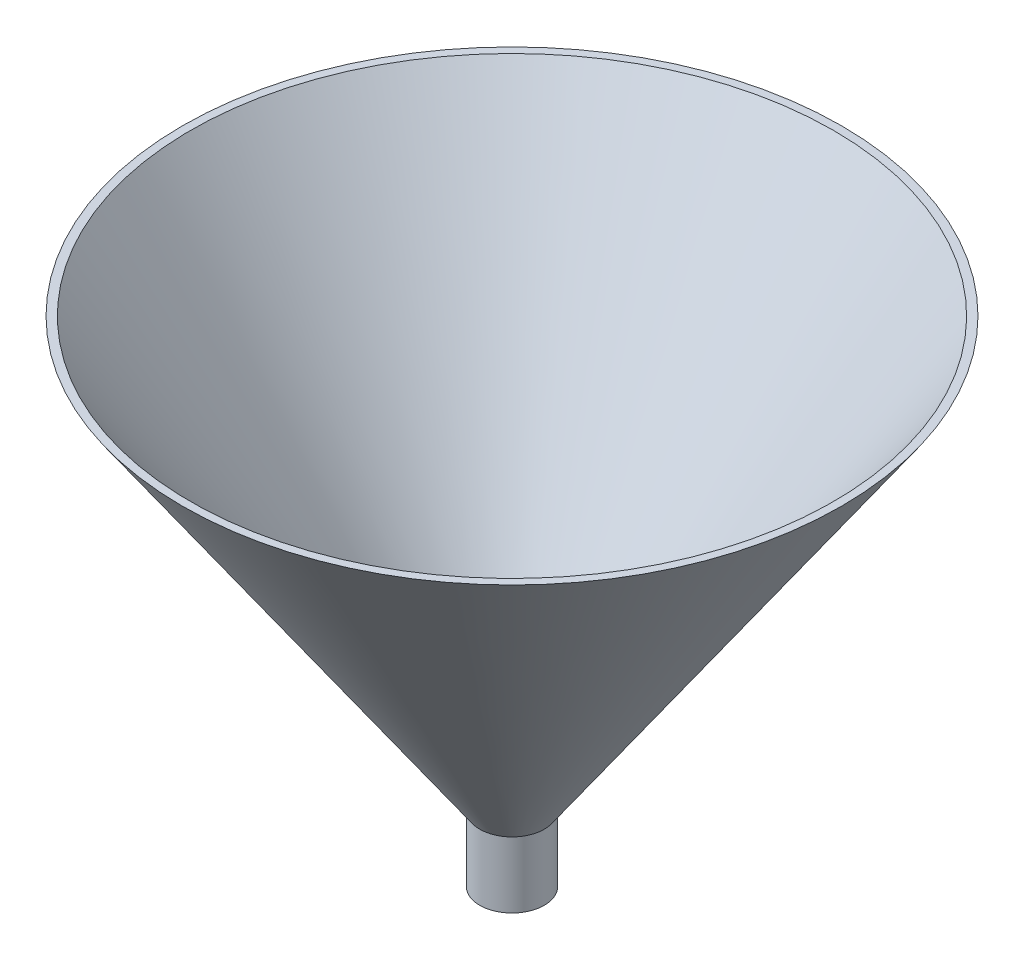
SolidWorks part; units mm, degrees
ref_plane "Front Plane" through (0, 0, 0) normal (0, 0, 1) x (1, 0, 0)
ref_plane "Top Plane" through (0, 0, 0) normal (0, 1, 0) x (1, 0, 0)
ref_plane "Right Plane" through (0, 0, 0) normal (1, 0, 0) x (0, 0, -1)
sketch "Sketch1" plane through (0, 0, 0) normal (1, 0, 0) x (0, 0, -1)
  line L0 (0, 0) -> (0, 75) construction
  line L1 (4.9, 0) -> (4.9, 10)
  line L2 (4.9, 10) -> (50, 75)
  point P5 (0, 0)
  point P7 (4.4126, 2.1305)
  point P8 (0, 0)
  dimension "D1" = 75
  dimension "D2" = 4.9
  dimension "D3" = 50
  dimension "D4" = 10
revolve "Revolve-Thin2" add sketch "Sketch1" angle 360 about L0 wall 1
sketch "Sketch2" plane through (0, 0, 0) normal (1, 0, 0) x (0, 0, -1)
  line L0 (49.1784, 75.5701) -> (-49.1784, 75.5701) construction
  line L1 (-50, 75) -> (50, 75)
  line L2 (-50, 75) -> (-50, 75.5701)
  line L3 (-50, 75.5701) -> (50, 75.5701)
  line L4 (50, 75) -> (50, 75.5701)
  point P5 (50, 100)
extrude "Cut-Extrude1" cut sketch "Sketch2" against normal through all both and the other way through all
